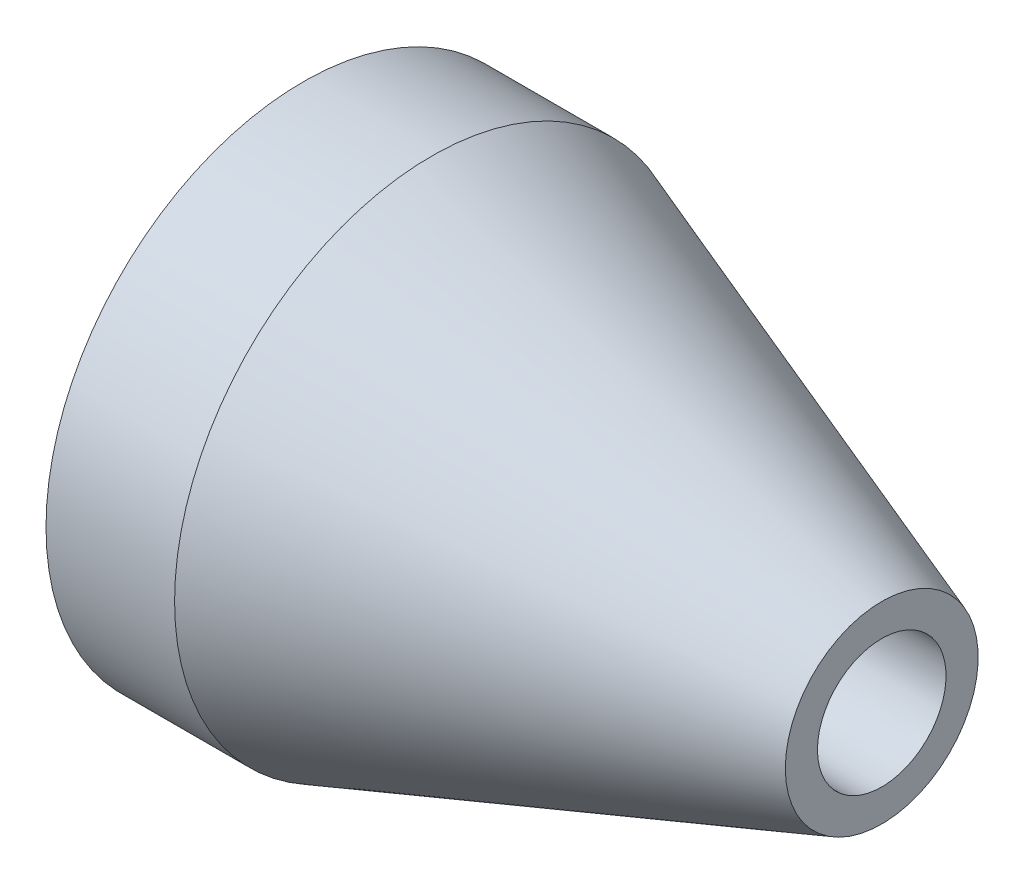
SolidWorks part; units mm, degrees
ref_plane "Front Plane" through (0, 0, 0) normal (0, 0, 1) x (1, 0, 0)
ref_plane "Top Plane" through (0, 0, 0) normal (0, 1, 0) x (1, 0, 0)
ref_plane "Right Plane" through (0, 0, 0) normal (1, 0, 0) x (0, 0, -1)
sketch "Sketch1" plane through (0, 0, 0) normal (0, 0, 1) x (1, 0, 0)
  line L0 (0, 0) -> (41.8112, 0) construction
  line L1 (0, -7.5) -> (0, -20)
  line L2 (0, -20) -> (10, -20)
  line L3 (10, -20) -> (45, -7.5)
  line L4 (0, -7.5) -> (0, -5)
  line L5 (45, -5) -> (0, -5)
  line L6 (45, -7.5) -> (45, -5)
  line L7 (59.433, -5) -> (-2.5, -5) construction
  line L9 (10.433, -22.5) -> (59.433, -5) construction
  line L10 (-2.5, -5) -> (-2.5, -22.5) construction
  line L11 (-2.5, -22.5) -> (10.433, -22.5) construction
  line L12 (45, -7.5) -> (0, -7.5) construction
  dimension "D1" = 40
  dimension "D2" = 2.5
  dimension "D3" = 10
  dimension "D4" = 15
revolve "Revolve1" add sketch "Sketch1" angle 360 about L0
